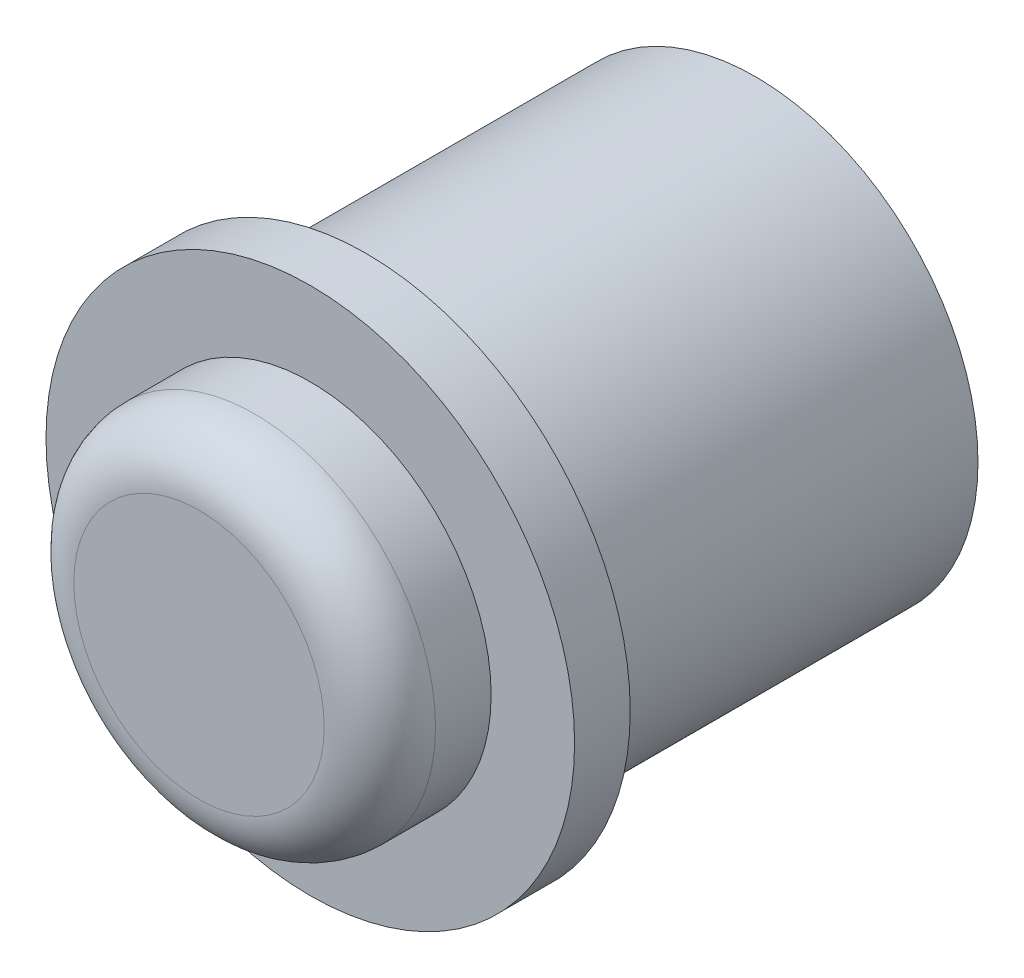
SolidWorks part; units mm, degrees
ref_plane "Front Plane" through (0, 0, 0) normal (0, 0, 1) x (1, 0, 0)
ref_plane "Top Plane" through (0, 0, 0) normal (0, 1, 0) x (1, 0, 0)
ref_plane "Right Plane" through (0, 0, 0) normal (1, 0, 0) x (0, 0, -1)
sketch "Sketch1" plane through (0, 0, 0) normal (0, 0, 1) x (1, 0, 0)
  circle A0 centre (0, 0) radius 8
  dimension "D1" = 16
extrude "Boss-Extrude1" add sketch "Sketch1" along normal blind 14
sketch "Sketch2" plane through (0, 0, 14) normal (0, 0, 1) x (1, 0, 0)
  circle A0 centre (0, 0) radius 9.5
  dimension "D1" = 19
extrude "Boss-Extrude2" add sketch "Sketch2" along normal blind 2
sketch "Sketch3" plane through (0, 0, 16) normal (0, 0, 1) x (1, 0, 0)
  circle A0 centre (0, 0) radius 6.5
  dimension "D1" = 13
extrude "Boss-Extrude3" add sketch "Sketch3" along normal blind 4
fillet "Fillet1" radius 2 1 edges at (6.5, 0, 20)
